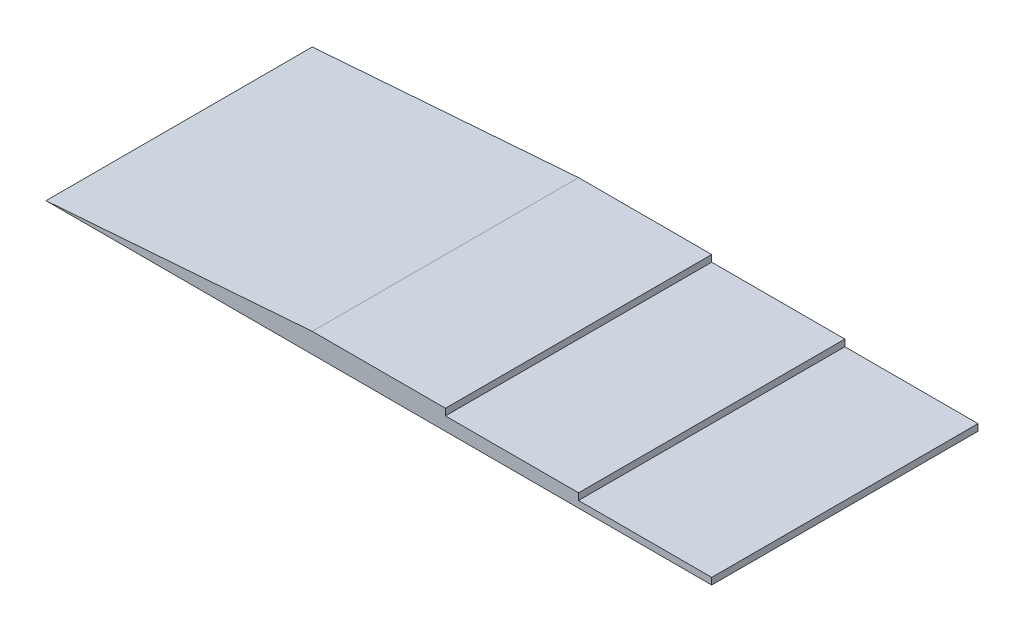
SolidWorks part; units mm, degrees
ref_plane "Front Plane" through (0, 0, 0) normal (0, 0, 1) x (1, 0, 0)
ref_plane "Top Plane" through (0, 0, 0) normal (0, 1, 0) x (1, 0, 0)
ref_plane "Right Plane" through (0, 0, 0) normal (1, 0, 0) x (0, 0, -1)
sketch "Sketch1" plane through (0, 0, 0) normal (0, 0, 1) x (1, 0, 0)
  line L12 (2000, 50) -> (1000, 50)
  line L13 (1000, 50) -> (1000, 100)
  line L14 (1000, 100) -> (0, 100)
  line L16 (2000, 50) -> (2000, 0)
  line L17 (2000, 0) -> (3000, 0)
  line L18 (0, 100) -> (0, -50)
  line L19 (0, -50) -> (3000, -50)
  line L20 (3000, -50) -> (3000, 0)
  line L26 (0, 100) -> (-2000, -50)
  line L28 (0, -50) -> (0, 150)
  line L31 (-2000, -50) -> (0, -50)
  dimension "D1" = 1000
  dimension "D2" = 1000
  dimension "D3" = 50
  dimension "D4" = 1000
  dimension "D5" = 50
  dimension "D6" = 50
  dimension "D7" = 2000
extrude "Boss-Extrude3" add sketch "Sketch1" against normal blind 2000 contours L19 L20 L17 L16 L12 L13 L14 L18 | L26 L31 L18
